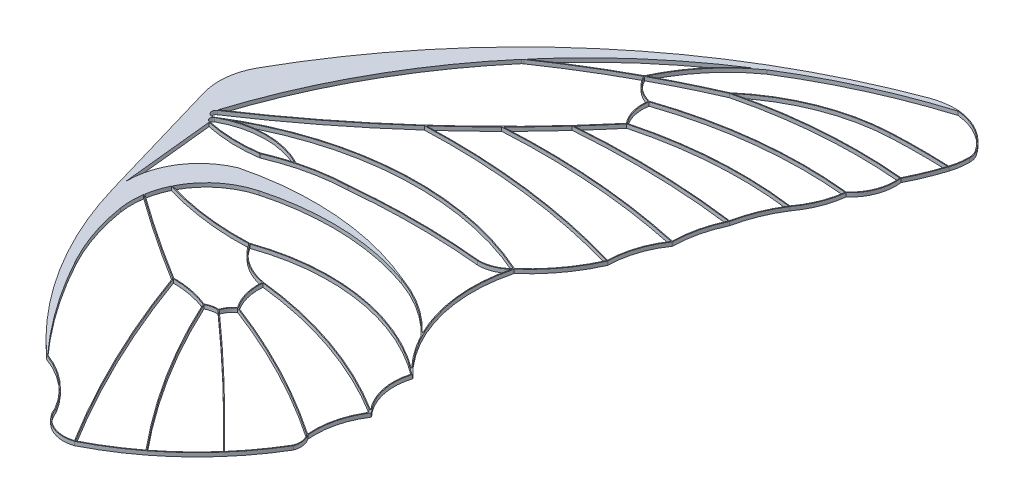
SolidWorks part; units mm, degrees
ref_plane "Plano frontal" through (0, 0, 0) normal (0, 0, 1) x (1, 0, 0)
ref_plane "Plano superior" through (0, 0, 0) normal (0, 1, 0) x (1, 0, 0)
ref_plane "Plano direito" through (0, 0, 0) normal (1, 0, 0) x (0, 0, -1)
sketch "Esboço1" plane through (0, 0, 0) normal (0, 1, 0) x (1, 0, 0)
  line L0 (245.8971, 320.852) -> (1229.6128, 320.852) construction
  line L1 (16.8906, -92.872) -> (-2.8919, -25.3314)
  line L3 (11.8593, -37.4647) -> (16.8906, -86.1328)
  arc A0 (-2.8919, -25.3314) -> (0, 0) centre (28.6286, -16.0991) cw
  arc A1 (0, 0) -> (189.3972, 162.1056) centre (316.3195, -177.8795) cw
  arc A3 (225.6385, 150.4697) -> (227.1081, 145.6019) centre (218.3116, 145.6019) cw construction
  arc A4 (227.1081, 145.6019) -> (225.6385, 136.1666) centre (196.0862, 145.6019) cw construction
  arc A5 (225.6385, 136.1666) -> (218.3116, 118.3563) centre (112.5985, 172.257) cw construction
  arc A7 (218.3116, 118.3563) -> (210.4763, 97.5461) centre (194.6459, 115.3865) cw construction
  arc A8 (210.4763, 97.5461) -> (202.0473, 76.5423) centre (166.9708, 102.8121) cw construction
  arc A9 (202.0473, 76.5423) -> (192.9964, 53.9892) centre (259.2241, 40.5039) ccw construction
  arc A10 (192.9964, 53.9892) -> (187.293, 29.7021) centre (245.6081, 28.8209) ccw construction
  arc A11 (187.293, 29.7021) -> (179.0373, 4.0907) centre (225.0788, 3.3859) ccw construction
  arc A12 (179.0373, 4.0907) -> (158.23, -24.0759) centre (104.6802, 37.2514) cw construction
  arc A15 (158.23, -24.0759) -> (13.4854, -32.4272) centre (93.7944, -165.8093) ccw construction
  arc A16 (158.23, -24.0759) -> (177.8517, -97.0522) centre (231.9136, -43.3901) ccw construction
  arc A17 (8.5132, -29.7405) -> (121.9031, 71.3535) centre (-285.6091, 414.2929) ccw construction
  arc A18 (11.0704, -33.894) -> (11.8796, -37.06) centre (11.8906, -35.3708) ccw
  arc A19 (69.7615, 17.5747) -> (179.0373, 4.0907) centre (83.0084, -324.6055) cw construction
  arc A20 (187.293, 29.7021) -> (90.5728, 37.2507) centre (111.635, -316.2908) ccw construction
  arc A21 (192.9964, 53.9892) -> (108.6142, 56.1566) centre (140.5341, -344.8129) ccw construction
  arc A22 (202.0473, 76.5423) -> (121.9031, 71.3535) centre (174.9731, -126.811) ccw construction
  arc A23 (121.9031, 71.3535) -> (117.6553, 87.2147) centre (137.0585, 83.9116) cw construction
  arc A24 (117.6553, 87.2147) -> (210.4763, 97.5461) centre (187.5432, -118.5488) cw construction
  arc A25 (202.7141, 163.713) -> (134.2312, 132.489) centre (289.7224, -117.8339) ccw
  arc A26 (65.7605, 73.6867) -> (134.9405, 112.1301) centre (303.5466, -272.7489) cw construction
  arc A27 (117.6553, 87.2147) -> (104.9295, 97.5363) centre (122.326, 105.9791) cw construction
  arc A28 (105.0708, 97.8389) -> (131.9285, 131.0439) centre (185.93, 59.9007) cw construction
  arc A29 (134.9405, 112.1301) -> (195.1764, 136.1273) centre (199.9365, 36.5807) cw construction
  arc A30 (134.9405, 112.1301) -> (218.3116, 118.3563) centre (194.9004, -129.4588) cw construction
  arc A31 (195.1764, 136.1273) -> (225.6385, 136.1666) centre (210.8302, -191.2388) cw construction
  arc A32 (164.2786, -78.4304) -> (163.8648, -78.0625) centre (76.6095, -176.6501) ccw construction
  arc A33 (40.2619, -50.4484) -> (16.8906, -86.1328) centre (54.6574, -85.3723) ccw
  arc A34 (11.8377, -37.2556) -> (39.3063, -38.1782) centre (28.1448, 38.8778) ccw construction
  arc A35 (39.3063, -38.1782) -> (77.0189, -29.7405) centre (80.4783, -133.7) cw construction
  arc A36 (77.0189, -29.7405) -> (145.0691, -29.7551) centre (110.9705, -372.2463) cw construction
  arc A37 (145.0691, -29.7551) -> (158.23, -24.0759) centre (145.2218, -12.02) ccw construction
  arc A38 (53.1607, -33.3342) -> (13.4854, -32.4272) centre (32.4211, -72.3358) ccw construction
  arc A39 (38.8997, -20.1148) -> (13.4854, -32.4272) centre (28.6163, -31.2738) cw construction
  arc A40 (16.8906, -92.872) -> (74.9246, -185.6146) centre (210.7556, -36.0892) ccw
  arc A41 (74.9929, -185.4267) -> (66.3816, -175.3804) centre (154.2645, -108.7641) cw construction
  arc A42 (39.4144, -134.6037) -> (75.0612, -185.2387) centre (266.3145, -12.7322) ccw
  arc A43 (74.9929, -185.4267) -> (101.4999, -207.5656) centre (57.6789, -233.0946) cw construction
  arc A44 (101.4999, -207.5656) -> (121.3412, -217.2503) centre (116.2629, -202.4873) ccw construction
  arc A45 (121.3412, -217.2503) -> (180.55, -161.9238) centre (55.9487, -87.924) ccw construction
  arc A46 (180.55, -161.9238) -> (179.3854, -153.5104) centre (171.7806, -158.8504) ccw construction
  arc A47 (179.3754, -98.5448) -> (185.959, -126.7273) centre (206.845, -106.9879) ccw construction
  arc A48 (185.959, -126.7273) -> (179.3854, -153.5104) centre (220.4313, -149.3865) ccw construction
  arc A49 (103.607, -114.0548) -> (179.3854, -153.5104) centre (-25.2756, -454.0845) cw construction
  arc A50 (55.95, -55.4784) -> (133.7088, -58.3585) centre (90.2455, -180.677) cw
  arc A51 (55.95, -55.4784) -> (31.1326, -75.9422) centre (66.32, -93.3351) ccw
  arc A52 (27.5649, -99.5565) -> (39.4144, -134.6037) centre (137.5319, -81.9033) ccw
  arc A53 (27.565, -87.1132) -> (73.2426, -117.5725) centre (461.4317, 514.0462) ccw construction
  arc A54 (73.2426, -117.5725) -> (92.998, -121.4212) centre (73.3114, -169.8452) cw construction
  arc A55 (92.998, -121.4212) -> (99.4217, -119.9985) centre (98.6915, -131.9152) cw construction
  arc A56 (99.4217, -119.9985) -> (103.607, -114.0548) centre (110.0937, -123.0679) cw construction
  arc A57 (103.607, -114.0548) -> (98.6915, -96.0121) centre (125.3192, -98.4486) cw construction
  arc A58 (98.6915, -96.0121) -> (77.4929, -81.9059) centre (103.8031, -65.3487) cw construction
  arc A59 (77.4929, -81.9059) -> (178.9645, -98.1504) centre (113.3271, -183.1111) cw construction
  arc A60 (77.4929, -81.9059) -> (31.0432, -76.1242) centre (71.4634, 59.1311) cw construction
  arc A61 (98.6915, -96.0121) -> (185.959, -126.7273) centre (76.8879, -297.2892) cw construction
  arc A62 (99.4217, -119.9985) -> (165.2455, -183.0853) centre (-749.6332, -1071.7733) cw construction
  arc A63 (92.998, -121.4212) -> (144.3602, -202.7494) centre (428.3218, 33.4673) ccw construction
  arc A64 (73.2426, -117.5725) -> (121.3412, -217.2503) centre (570.6991, 61.0271) ccw construction
  arc A65 (8.6464, -29.8922) -> (10.8842, -33.7922) centre (9.8905, -31.7703) ccw
  arc A66 (65.8737, 73.5218) -> (65.1633, 72.9862) centre (71.5226, 65.2919) ccw
  arc A67 (104.7763, 97.681) -> (130.1059, 129.8789) centre (185.93, 59.9007) cw
  arc A68 (104.7481, 97.6206) -> (150.4255, 142.0756) centre (185.93, 59.9007) cw construction
  arc A69 (104.9295, 97.5363) -> (150.5048, 141.892) centre (185.93, 59.9007) cw construction
  arc A70 (130.1059, 129.8789) -> (66.2643, 74.2743) centre (289.7224, -117.8339) ccw
  arc A71 (65.1633, 72.9862) -> (8.6083, -29.4376) centre (289.7224, -117.8339) ccw
  arc A72 (135.7135, 112.5265) -> (195.186, 135.9275) centre (199.9365, 36.5807) cw
  arc A73 (134.8328, 112.3013) -> (195.1668, 136.3271) centre (199.9365, 36.5807) cw
  arc A74 (65.8737, 73.5218) -> (104.8415, 97.2621) centre (303.5466, -272.7489) cw
  arc A75 (66.2643, 74.2743) -> (104.7763, 97.681) centre (303.5466, -272.7489) cw
  arc A76 (105.3664, 97.9971) -> (134.2312, 132.489) centre (185.93, 59.9007) cw
  arc A77 (105.3664, 97.9971) -> (134.8328, 112.3013) centre (303.5466, -272.7489) cw
  arc A78 (65.6474, 73.8516) -> (134.8603, 112.3133) centre (303.5466, -272.7489) cw construction
  arc A79 (203.4113, 163.9275) -> (225.6385, 150.4697) centre (200.23, 133.5888) cw construction
  arc A80 (203.3904, 163.7286) -> (225.4719, 150.359) centre (200.23, 133.5888) cw
  arc A81 (203.4321, 164.1264) -> (225.805, 150.5804) centre (200.23, 133.5888) cw
  arc A82 (189.3972, 162.1056) -> (203.4321, 164.1264) centre (201.0573, 130.8716) cw
  arc A83 (203.3904, 163.7286) -> (202.7141, 163.713) centre (203.1131, 161.0838) ccw
  arc A84 (225.4719, 150.359) -> (226.9081, 145.6019) centre (218.3116, 145.6019) cw
  arc A85 (226.9081, 145.6019) -> (225.4941, 136.3733) centre (196.0862, 145.6019) cw
  arc A86 (225.805, 150.5804) -> (227.3081, 145.6019) centre (218.3116, 145.6019) cw
  arc A87 (227.3081, 145.6019) -> (225.829, 136.1058) centre (196.0862, 145.6019) cw
  arc A88 (195.186, 135.9275) -> (225.3682, 135.9786) centre (210.8302, -191.2388) cw
  arc A89 (195.1668, 136.3271) -> (225.4941, 136.3733) centre (210.8302, -191.2388) cw
  arc A90 (195.1668, 136.3271) -> (225.6475, 136.3664) centre (210.8302, -191.2388) cw construction
  arc A91 (226.9081, 145.6019) -> (225.4479, 136.2275) centre (196.0862, 145.6019) cw construction
  arc A92 (225.3682, 135.9786) -> (218.195, 118.5681) centre (112.5985, 172.257) cw
  arc A93 (135.0052, 111.9401) -> (218.1326, 118.1722) centre (194.9004, -129.4588) cw
  arc A94 (218.1326, 118.1722) -> (210.4094, 97.7543) centre (194.6459, 115.3865) cw
  arc A95 (225.829, 136.1058) -> (218.5176, 118.3201) centre (112.5985, 172.257) cw
  arc A96 (135.7135, 112.5265) -> (218.195, 118.5681) centre (194.9004, -129.4588) cw
  arc A97 (218.5176, 118.3201) -> (210.6657, 97.4469) centre (194.6459, 115.3865) cw
  arc A98 (225.4479, 136.2275) -> (218.1334, 118.4471) centre (112.5985, 172.257) cw construction
  arc A99 (134.8923, 112.3242) -> (218.3304, 118.5554) centre (194.9004, -129.4588) cw construction
  arc A100 (195.186, 135.9275) -> (225.6294, 135.9669) centre (210.8302, -191.2388) cw construction
  arc A101 (134.8101, 112.2817) -> (195.1668, 136.3271) centre (199.9365, 36.5807) cw construction
  arc A102 (135.0709, 111.9785) -> (195.186, 135.9275) centre (199.9365, 36.5807) cw construction
  arc A103 (134.9887, 111.936) -> (218.2928, 118.1572) centre (194.9004, -129.4588) cw construction
  arc A104 (65.8737, 73.5218) -> (135.0208, 111.9469) centre (303.5466, -272.7489) cw construction
  arc A105 (218.51, 118.3812) -> (210.6091, 97.3965) centre (194.6459, 115.3865) cw construction
  arc A106 (225.829, 136.1058) -> (218.4898, 118.2654) centre (112.5985, 172.257) cw construction
  arc A107 (218.1131, 118.3314) -> (210.3436, 97.6957) centre (194.6459, 115.3865) cw construction
  arc A108 (117.6468, 87.423) -> (105.1942, 97.4512) centre (122.326, 105.9791) cw
  arc A109 (121.9757, 71.58) -> (117.8329, 87.0637) centre (137.0585, 83.9116) cw
  arc A110 (117.8329, 87.0637) -> (210.2529, 97.3685) centre (187.5432, -118.5488) cw
  arc A111 (210.2529, 97.3685) -> (201.9573, 76.7561) centre (166.9708, 102.8121) cw
  arc A112 (117.428, 87.066) -> (104.8415, 97.2621) centre (122.326, 105.9791) cw
  arc A113 (121.643, 71.3551) -> (117.428, 87.066) centre (137.0585, 83.9116) cw
  arc A114 (117.6468, 87.423) -> (210.4094, 97.7543) centre (187.5432, -118.5488) cw
  arc A115 (210.6657, 97.4469) -> (202.2122, 76.4289) centre (166.9708, 102.8121) cw
  arc A116 (105.1942, 97.4512) -> (135.0052, 111.9401) centre (303.5466, -272.7489) cw
  arc A117 (117.607, 87.0206) -> (104.7496, 97.449) centre (122.326, 105.9791) cw construction
  arc A118 (117.7036, 87.4087) -> (105.1094, 97.6236) centre (122.326, 105.9791) cw construction
  arc A119 (121.7491, 71.2259) -> (117.4582, 87.2482) centre (137.0585, 83.9116) cw construction
  arc A120 (117.7197, 87.0253) -> (210.2529, 97.3685) centre (187.5432, -118.5488) cw construction
  arc A121 (122.0571, 71.4811) -> (117.8525, 87.1811) centre (137.0585, 83.9116) cw construction
  arc A122 (117.591, 87.404) -> (210.6988, 97.7235) centre (187.5432, -118.5488) cw construction
  arc A123 (201.7125, 76.3849) -> (192.8379, 54.2118) centre (259.2241, 40.5039) ccw
  arc A124 (210.6988, 97.7235) -> (202.2073, 76.4225) centre (166.9708, 102.8121) cw construction
  arc A125 (202.2122, 76.4289) -> (193.1924, 53.9493) centre (259.2241, 40.5039) ccw
  arc A126 (201.9573, 76.7561) -> (121.9757, 71.58) centre (174.9731, -126.811) ccw
  arc A127 (193.1924, 53.9493) -> (193.1768, 53.9029) centre (192.9964, 53.9892) cw
  arc A128 (8.6464, -29.8922) -> (69.8412, 17.3776) centre (-285.6091, 414.2929) ccw
  arc A129 (8.6083, -29.4376) -> (121.643, 71.3551) centre (-285.6091, 414.2929) ccw
  arc A130 (192.8379, 54.2118) -> (109.1013, 56.3957) centre (140.5341, -344.8129) ccw
  arc A131 (202.2165, 76.4357) -> (193.1924, 53.9493) centre (259.2241, 40.5039) ccw construction
  arc A132 (8.4027, -29.5738) -> (121.7501, 71.4823) centre (-285.6091, 414.2929) ccw construction
  arc A133 (202.0737, 76.7406) -> (121.8513, 71.5467) centre (174.9731, -126.811) ccw construction
  arc A134 (187.0972, 29.9495) -> (91.0867, 37.4813) centre (111.635, -316.2908) ccw
  arc A135 (8.6236, -29.9073) -> (122.0561, 71.2247) centre (-285.6091, 414.2929) ccw construction
  arc A136 (193.0225, 54.1875) -> (108.5983, 56.356) centre (140.5341, -344.8129) ccw construction
  arc A137 (69.8412, 17.3776) -> (178.761, 3.963) centre (83.0084, -324.6055) cw
  arc A138 (109.1013, 56.3957) -> (122.0156, 71.1766) centre (-285.6091, 414.2929) ccw
  arc A139 (201.8781, 76.649) -> (192.8004, 54.0291) centre (259.2241, 40.5039) ccw construction
  arc A140 (210.2529, 97.3685) -> (201.8872, 76.6622) centre (166.9708, 102.8121) cw construction
  arc A141 (201.7125, 76.3849) -> (122.0156, 71.1766) centre (174.9731, -126.811) ccw
  arc A142 (193.1768, 53.9029) -> (187.4952, 29.8402) centre (245.6081, 28.8209) ccw
  arc A143 (187.3768, 29.4721) -> (187.4952, 29.8402) centre (186.8279, 29.8519) ccw
  arc A144 (187.0972, 29.9495) -> (90.5609, 37.4504) centre (111.635, -316.2908) ccw construction
  arc A145 (91.0867, 37.4813) -> (108.709, 55.9635) centre (-285.6091, 414.2929) ccw
  arc A146 (187.4898, 29.4542) -> (90.5847, 37.0511) centre (111.635, -316.2908) ccw construction
  arc A147 (192.6977, 53.8267) -> (187.0972, 29.9495) centre (245.6081, 28.8209) ccw
  arc A148 (192.816, 54.0755) -> (187.0972, 29.9495) centre (245.6081, 28.8209) ccw construction
  arc A149 (192.6977, 53.8267) -> (108.709, 55.9635) centre (140.5341, -344.8129) ccw
  arc A150 (187.3768, 29.4721) -> (179.2373, 4.0876) centre (225.0788, 3.3859) ccw
  arc A151 (70.3073, 17.7955) -> (178.8421, 4.356) centre (83.0084, -324.6055) cw
  arc A152 (186.9587, 29.5703) -> (178.8421, 4.356) centre (225.0788, 3.3859) ccw
  arc A153 (69.7538, 17.7745) -> (178.8421, 4.356) centre (83.0084, -324.6055) cw construction
  arc A154 (70.3073, 17.7955) -> (90.6603, 37.0556) centre (-285.6091, 414.2929) ccw
  arc A155 (69.7692, 17.3748) -> (179.2341, 3.8248) centre (83.0084, -324.6055) cw construction
  arc A156 (187.1288, 29.8164) -> (178.8421, 4.356) centre (225.0788, 3.3859) ccw construction
  arc A157 (186.9587, 29.5703) -> (90.6603, 37.0556) centre (111.635, -316.2908) ccw
  arc A158 (187.4571, 29.5878) -> (179.2341, 3.8248) centre (225.0788, 3.3859) ccw construction
  arc A159 (193.1768, 53.9029) -> (187.4898, 29.4542) centre (245.6081, 28.8209) ccw construction
  arc A160 (178.8547, 4.1721) -> (178.8436, 4.1472) centre (104.6802, 37.2514) cw
  arc A161 (158.1953, -23.8405) -> (10.8842, -33.7922) centre (93.7944, -165.8093) ccw
  arc A162 (179.22, 4.0092) -> (158.4079, -24.186) centre (104.6802, 37.2514) cw
  arc A163 (179.22, 4.0092) -> (158.2644, -24.3113) centre (104.6802, 37.2514) cw construction
  arc A165 (158.1953, -23.8405) -> (13.3822, -32.2559) centre (93.7944, -165.8093) ccw construction
  arc A167 (53.1846, -33.1205) -> (16.3441, -30.9777) centre (32.4211, -72.3358) ccw
  arc A168 (11.8593, -37.4647) -> (39.3612, -38.3724) centre (28.1448, 38.8778) ccw
  arc A169 (39.3612, -38.3724) -> (77.0321, -29.9402) centre (80.4783, -133.7) cw
  arc A170 (77.0321, -29.9402) -> (145.0582, -29.9551) centre (110.9705, -372.2463) cw
  arc A171 (145.0582, -29.9551) -> (157.8482, -24.7583) centre (145.2218, -12.02) ccw
  arc A172 (145.0582, -29.9551) -> (158.3767, -24.2119) centre (145.2218, -12.02) ccw construction
  arc A173 (11.8796, -37.06) -> (39.2515, -37.9841) centre (28.1448, 38.8778) ccw
  arc A174 (39.2515, -37.9841) -> (52.6186, -33.2758) centre (80.4783, -133.7) cw
  arc A175 (77.0057, -29.5409) -> (145.0798, -29.5552) centre (110.9705, -372.2463) cw
  arc A176 (145.0798, -29.5552) -> (157.8927, -24.1424) centre (145.2218, -12.02) ccw
  arc A177 (53.2546, -33.1576) -> (13.3997, -32.2465) centre (32.4211, -72.3358) ccw construction
  arc A178 (11.7958, -37.4511) -> (39.3612, -38.3724) centre (28.1448, 38.8778) ccw construction
  arc A179 (158.2644, -24.3113) -> (13.5886, -32.5986) centre (93.7944, -165.8093) ccw construction
  arc A180 (145.0798, -29.5552) -> (158.0833, -23.94) centre (145.2218, -12.02) ccw construction
  arc A182 (52.6186, -33.2758) -> (11.0704, -33.894) centre (32.4211, -72.3358) ccw
  arc A183 (53.1846, -33.1205) -> (77.0057, -29.5409) centre (80.4783, -133.7) cw
  arc A184 (39.2515, -37.9841) -> (77.0057, -29.5409) centre (80.4783, -133.7) cw construction
  arc A185 (157.8927, -24.1424) -> (16.3441, -30.9777) centre (93.7944, -165.8093) ccw
  arc A186 (178.761, 3.963) -> (158.1953, -23.8405) centre (104.6802, 37.2514) cw
  arc A187 (178.8547, 4.1721) -> (158.1953, -23.8405) centre (104.6802, 37.2514) cw construction
  arc A188 (179.22, 4.0092) -> (179.2373, 4.0876) centre (179.0373, 4.0907) ccw
  arc A189 (157.8482, -24.7583) -> (163.5415, -77.4206) centre (231.9136, -43.3901) ccw
  arc A190 (158.4079, -24.186) -> (179.5133, -98.4) centre (231.9136, -43.3901) ccw
  arc A191 (158.0365, -24.0252) -> (179.2374, -98.6896) centre (231.9136, -43.3901) ccw construction
  arc A192 (133.8427, -57.9816) -> (40.2619, -50.4484) centre (75.882, -192.9794) ccw
  arc A193 (158.4235, -24.1266) -> (179.5133, -98.4) centre (231.9136, -43.3901) ccw construction
  arc A194 (133.7758, -58.17) -> (163.8648, -78.0625) centre (108.6533, -128.872) cw construction
  arc A195 (133.7088, -58.3585) -> (163.7246, -78.2055) centre (108.6533, -128.872) cw
  arc A196 (163.7246, -78.2055) -> (164.2392, -78.7877) centre (149.3526, -91.428) cw
  arc A197 (133.8427, -57.9816) -> (163.5415, -77.4206) centre (108.6533, -128.872) cw
  arc A198 (77.3856, -82.1106) -> (30.9549, -76.3065) centre (71.4634, 59.1311) cw
  arc A199 (133.8427, -57.9816) -> (164.005, -77.9196) centre (108.6533, -128.872) cw construction
  arc A200 (164.1455, -78.5796) -> (163.7246, -78.2055) centre (76.6095, -176.6501) ccw construction
  arc A201 (164.2392, -78.7877) -> (176.8413, -96.3038) centre (231.9136, -43.3901) ccw
  arc A202 (164.4118, -78.2811) -> (164.005, -77.9196) centre (76.6095, -176.6501) ccw construction
  arc A203 (77.7964, -82.0109) -> (178.8422, -98.3087) centre (113.3271, -183.1111) cw
  arc A204 (77.4544, -81.7073) -> (31.1326, -75.9422) centre (71.4634, 59.1311) cw
  arc A205 (77.4544, -81.7073) -> (176.8413, -96.3038) centre (113.3271, -183.1111) cw
  arc A206 (77.5314, -82.1044) -> (30.986, -76.3158) centre (71.4634, 59.1311) cw construction
  arc A207 (30.9549, -76.3065) -> (27.6041, -86.8743) centre (66.32, -93.3351) ccw
  arc A208 (77.4544, -81.7073) -> (31.1005, -75.9326) centre (71.4634, 59.1311) cw construction
  arc A209 (158.23, -24.0759) -> (179.3754, -98.5448) centre (231.9136, -43.3901) ccw construction
  arc A210 (98.7187, -95.8139) -> (77.7964, -82.0109) centre (103.8031, -65.3487) cw
  arc A211 (103.7344, -113.8892) -> (98.8729, -96.233) centre (125.3192, -98.4486) cw
  arc A212 (98.713, -95.8133) -> (184.8389, -125.7798) centre (76.8879, -297.2892) cw construction
  arc A213 (179.5665, -98.6035) -> (185.9696, -126.4464) centre (206.845, -106.9879) ccw
  arc A214 (98.4761, -96.1784) -> (77.3856, -82.1106) centre (103.8031, -65.3487) cw
  arc A215 (103.3296, -114.0103) -> (98.4761, -96.1784) centre (125.3192, -98.4486) cw
  arc A216 (98.7187, -95.8139) -> (184.8389, -125.7798) centre (76.8879, -297.2892) cw
  arc A217 (179.5133, -98.4) -> (179.5665, -98.6035) centre (179.3754, -98.5448) cw
  arc A218 (98.6586, -96.2094) -> (77.3236, -82.0124) centre (103.8031, -65.3487) cw construction
  arc A219 (77.5314, -82.1044) -> (178.8422, -98.3087) centre (113.3271, -183.1111) cw construction
  arc A220 (178.8422, -98.3087) -> (179.0485, -98.9406) centre (178.4809, -98.7763) cw
  arc A221 (98.7244, -95.8148) -> (77.6621, -81.7994) centre (103.8031, -65.3487) cw construction
  arc A222 (77.4544, -81.7073) -> (179.0867, -97.9922) centre (113.3271, -183.1111) cw construction
  arc A223 (99.6493, -119.9335) -> (103.6372, -114.2802) centre (110.0937, -123.0679) cw
  arc A224 (179.0485, -98.9406) -> (184.8389, -125.7798) centre (206.845, -106.9879) ccw
  arc A225 (179.1842, -98.486) -> (184.8389, -125.7798) centre (206.845, -106.9879) ccw construction
  arc A226 (103.6372, -114.2802) -> (179.2425, -153.6551) centre (-25.2756, -454.0845) cw
  arc A227 (186.018, -127.0026) -> (179.5792, -153.4387) centre (220.4313, -149.3865) ccw
  arc A228 (99.2747, -119.7902) -> (103.3296, -114.0103) centre (110.0937, -123.0679) cw
  arc A229 (103.7344, -113.8892) -> (179.1459, -153.1057) centre (-25.2756, -454.0845) cw
  arc A230 (185.7919, -126.6175) -> (185.7905, -126.6196) centre (220.4313, -149.3865) ccw
  arc A231 (184.6648, -128.4325) -> (179.1459, -153.1057) centre (220.4313, -149.3865) ccw
  arc A232 (185.7919, -126.6175) -> (179.1459, -153.1057) centre (220.4313, -149.3865) ccw construction
  arc A233 (186.1262, -126.8372) -> (179.6297, -153.919) centre (220.4313, -149.3865) ccw construction
  arc A234 (98.6699, -96.2109) -> (187.474, -127.9445) centre (76.8879, -297.2892) cw construction
  arc A235 (186.018, -127.0026) -> (185.9696, -126.4464) centre (185.6381, -126.7554) ccw
  arc A236 (179.5665, -98.6035) -> (187.474, -127.9445) centre (206.845, -106.9879) ccw construction
  arc A237 (184.6648, -128.4325) -> (183.9983, -125.7249) centre (182.9391, -127.4215) ccw
  arc A238 (93.2588, -121.5089) -> (99.3405, -120.1941) centre (98.6915, -131.9152) cw
  arc A239 (99.3405, -120.1941) -> (164.9738, -183.0926) centre (-749.6332, -1071.7733) cw
  arc A240 (121.4315, -217.4287) -> (180.7321, -162.0089) centre (55.9487, -87.924) ccw
  arc A241 (180.7321, -162.0089) -> (179.5792, -153.4387) centre (171.7806, -158.8504) ccw
  arc A242 (92.986, -121.2005) -> (99.2747, -119.7902) centre (98.6915, -131.9152) cw
  arc A243 (99.6493, -119.9335) -> (165.2373, -182.7899) centre (-749.6332, -1071.7733) cw
  arc A244 (121.4146, -216.9889) -> (144.0736, -202.7175) centre (55.9487, -87.924) ccw
  arc A245 (180.3678, -161.8389) -> (179.2425, -153.6551) centre (171.7806, -158.8504) ccw
  arc A246 (99.2295, -119.9432) -> (103.578, -113.83) centre (110.0937, -123.0679) cw construction
  arc A247 (103.578, -113.83) -> (179.1459, -153.1057) centre (-25.2756, -454.0845) cw construction
  arc A248 (92.9026, -121.2454) -> (99.5034, -119.8034) centre (98.6915, -131.9152) cw construction
  arc A249 (99.6139, -120.0538) -> (103.6372, -114.2802) centre (110.0937, -123.0679) cw construction
  arc A250 (99.5034, -119.8034) -> (165.389, -182.9459) centre (-749.6332, -1071.7733) cw construction
  arc A251 (103.7694, -113.9381) -> (98.8906, -96.0303) centre (125.3192, -98.4486) cw construction
  arc A252 (103.4446, -114.1716) -> (98.4923, -95.9939) centre (125.3192, -98.4486) cw construction
  arc A253 (180.3678, -161.8389) -> (179.2217, -153.6253) centre (171.7806, -158.8504) ccw construction
  arc A254 (98.8729, -96.233) -> (183.9983, -125.7249) centre (76.8879, -297.2892) cw
  arc A255 (103.6372, -114.2802) -> (179.6297, -153.919) centre (-25.2756, -454.0845) cw construction
  arc A256 (180.7321, -162.0089) -> (179.549, -153.3955) centre (171.7806, -158.8504) ccw construction
  arc A257 (165.3772, -182.9338) -> (165.389, -182.9459) centre (-749.6332, -1071.7733) cw
  arc A258 (165.2373, -182.7899) -> (180.3678, -161.8389) centre (55.9487, -87.924) ccw
  arc A259 (121.251, -217.0718) -> (180.3678, -161.8389) centre (55.9487, -87.924) ccw construction
  arc A260 (99.3405, -120.1941) -> (165.102, -183.2246) centre (-749.6332, -1071.7733) cw construction
  arc A261 (121.4315, -217.4287) -> (121.4146, -217.4365) centre (121.315, -217.1984) cw
  arc A262 (92.8496, -121.5768) -> (144.0736, -202.7175) centre (428.3218, 33.4673) ccw
  arc A263 (73.2991, -117.3724) -> (92.986, -121.2005) centre (73.3114, -169.8452) cw
  arc A264 (93.2588, -121.5089) -> (144.3907, -202.4733) centre (428.3218, 33.4673) ccw
  arc A265 (73.2423, -117.3725) -> (93.1465, -121.2657) centre (73.3114, -169.8452) cw construction
  arc A266 (93.1465, -121.2657) -> (144.5139, -202.6215) centre (428.3218, 33.4673) ccw construction
  arc A267 (93.0933, -121.597) -> (99.3405, -120.1941) centre (98.6915, -131.9152) cw construction
  arc A268 (144.3907, -202.4733) -> (164.9738, -183.0926) centre (55.9487, -87.924) ccw
  arc A269 (74.9246, -185.6146) -> (101.3172, -207.6494) centre (57.6789, -233.0946) cw
  arc A270 (92.8496, -121.5768) -> (144.2064, -202.8773) centre (428.3218, 33.4673) ccw construction
  arc A271 (101.3172, -207.6494) -> (121.4146, -217.4365) centre (116.2629, -202.4873) ccw
  arc A272 (73.5271, -117.7729) -> (121.4146, -216.9889) centre (570.6991, 61.0271) ccw
  arc A273 (27.682, -86.951) -> (73.2991, -117.3724) centre (461.4317, 514.0462) ccw
  arc A274 (75.0612, -185.2387) -> (101.6826, -207.482) centre (57.6789, -233.0946) cw
  arc A275 (101.6826, -207.482) -> (121.0383, -217.1408) centre (116.2629, -202.4873) ccw
  arc A276 (73.0781, -117.7061) -> (121.0383, -217.1408) centre (570.6991, 61.0271) ccw
  arc A277 (27.5301, -87.3346) -> (73.0781, -117.7061) centre (461.4317, 514.0462) ccw
  arc A278 (27.682, -86.951) -> (27.6041, -86.8743) centre (27.8932, -86.6584) cw
  arc A279 (27.5301, -87.3346) -> (27.5649, -99.5565) centre (66.32, -93.3351) ccw
  arc A280 (27.4479, -87.2753) -> (73.0781, -117.7061) centre (461.4317, 514.0462) ccw construction
  arc A281 (27.682, -86.951) -> (73.4071, -117.4388) centre (461.4317, 514.0462) ccw construction
  arc A282 (73.4071, -117.4388) -> (121.6421, -217.3562) centre (570.6991, 61.0271) ccw construction
  arc A283 (73.5271, -117.7729) -> (92.8496, -121.5768) centre (73.3114, -169.8452) cw
  arc A284 (73.2428, -117.7725) -> (92.8496, -121.5768) centre (73.3114, -169.8452) cw construction
  arc A285 (101.3172, -207.6494) -> (121.6421, -217.3562) centre (116.2629, -202.4873) ccw construction
  dimension "D2" = 0.2
  dimension "D3" = 0.2
  dimension "D4" = 0.2
  dimension "D5" = 0.2
  dimension "D41" = 2
  dimension "D1" = 230
  dimension "D6" = 0.2
  dimension "D7" = 0.2
  dimension "D8" = 0.2
  dimension "D9" = 0.2
  dimension "D10" = 0.2
  dimension "D11" = 0.2
  dimension "D12" = 0.2
  dimension "D13" = 0.2
  dimension "D14" = 0.2
  dimension "D15" = 0.2
  dimension "D16" = 0.2
  dimension "D17" = 0.2
  dimension "D18" = 0.2
  dimension "D19" = 0.2
  dimension "D20" = 0.2
  dimension "D21" = 0.2
  dimension "D22" = 0.2
  dimension "D23" = 0.2
  dimension "D24" = 0.2
  dimension "D25" = 0.2
  dimension "D26" = 0.2
  dimension "D27" = 0.2
  dimension "D28" = 0.2
  dimension "D29" = 0.2
  dimension "D30" = 0.2
  dimension "D31" = 0.2
  dimension "D32" = 0.2
  dimension "D33" = 0.2
  dimension "D34" = 0.2
  dimension "D35" = 0.2
  dimension "D36" = 0.2
  dimension "D37" = 0.2
  dimension "D38" = 0.2
  dimension "D39" = 0.2
  dimension "D40" = 0.2
  dimension "D42" = 0.2
  dimension "D43" = 0.2
  dimension "D44" = 0.2
  dimension "D45" = 0.2
  dimension "D46" = 0.2
  dimension "D47" = 0.2
extrude "Ressalto-extrusão1" add sketch "Esboço1" along normal blind 2
